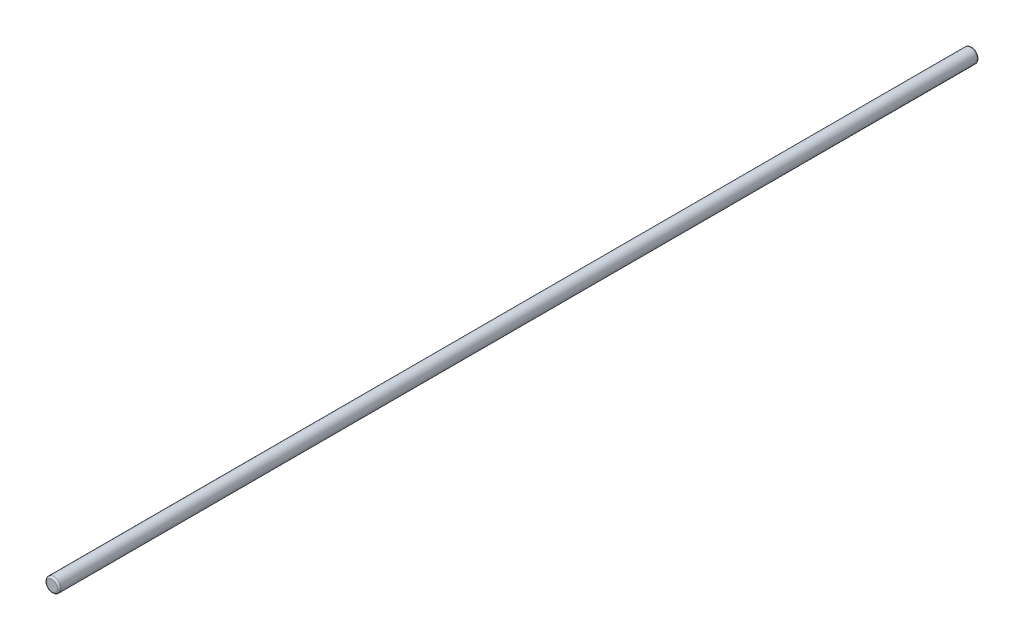
SolidWorks part; units mm, degrees
ref_plane "正面" through (0, 0, 0) normal (0, 0, 1) x (1, 0, 0)
ref_plane "平面" through (0, 0, 0) normal (0, 1, 0) x (1, 0, 0)
ref_plane "右側面" through (0, 0, 0) normal (1, 0, 0) x (0, 0, -1)
sketch "ｽｹｯﾁ1" plane through (0, 0, 0) normal (0, 0, 1) x (1, 0, 0)
  circle A0 centre (0, 0) radius 4
  dimension "D1" = 8
extrude "ﾎﾞｽ - 押し出し1" add sketch "ｽｹｯﾁ1" along normal blind 520
fillet "ﾌｨﾚｯﾄ1" radius 1 1 edges at (4, 0, 520)
fillet "ﾌｨﾚｯﾄ2" radius 1 1 edges at (4, 0, 0)
